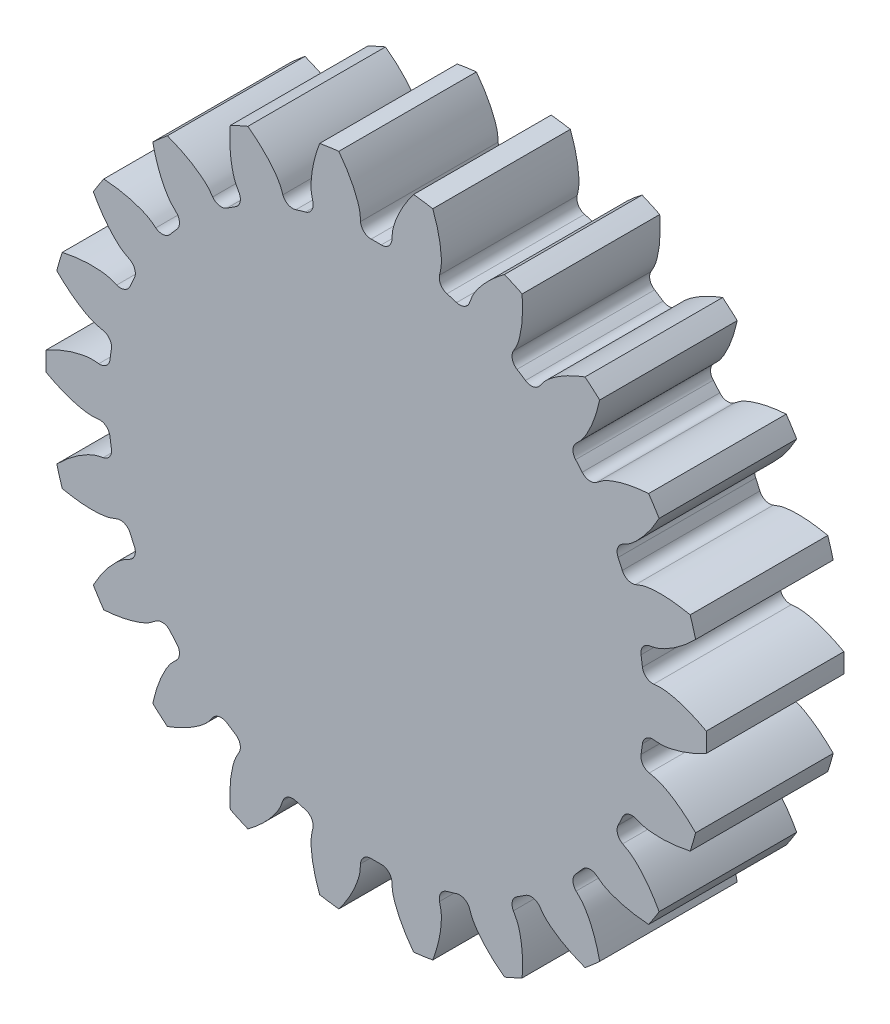
SolidWorks part; units mm, degrees
ref_plane "前视基准面" through (0, 0, 0) normal (0, 0, 1) x (1, 0, 0)
ref_plane "上视基准面" through (0, 0, 0) normal (0, 1, 0) x (1, 0, 0)
ref_plane "右视基准面" through (0, 0, 0) normal (1, 0, 0) x (0, 0, -1)
ref_axis "Axis1" through (0, 0, -88.99) along (0, 0, 1)
sketch "草图1" plane through (0, 0, 0) normal (0, 0, 1) x (1, 0, 0)
  circle A0 centre (0, 0) radius 12
extrude "LaShenA" add sketch "草图1" along normal blind 5
sketch "SketchA" plane through (0, 0, 5) normal (0, 0, 1) x (1, 0, 0)
  line L0 (0, 0) -> (0, 12) construction
  arc A0 (0.1829, 9.7483) -> (-0.1829, 9.7483) centre (0, 0) ccw
  arc A1 (1.7922, 12.4394) -> (-1.7922, 12.4394) centre (0, 0) ccw
  arc A2 (-0.1829, 9.7483) -> (-0.5693, 10.1058) centre (-0.19, 10.1282) cw
  arc A3 (0.5693, 10.1058) -> (0.1829, 9.7483) centre (0.19, 10.1282) cw
  circle A4 centre (0, 0) radius 10.3366 construction
  circle A5 centre (0, 0) radius 12 construction
  circle A6 centre (0, 0) radius 9.75 construction
  circle A7 centre (0, 0) radius 11 construction
  spline S0 degree 3 poles (0.5693, 10.1058) (0.5736, 10.1777) (0.5776, 10.2793) (0.5937, 10.3939) (0.606, 10.4523) (0.6168, 10.4986) (0.6308, 10.5517) (0.6482, 10.6114) (0.6693, 10.6775) (0.6947, 10.75) (0.7246, 10.8287) (0.7593, 10.9132) (0.7992, 11.0036) (0.8447, 11.0994) (0.8959, 11.2005) (0.9533, 11.3067) (1.0172, 11.4176) (1.0878, 11.533) (1.1655, 11.6527) (1.2504, 11.7762) (1.3429, 11.9034) (1.4432, 12.0339) (1.5907, 12.2156) (1.7093, 12.3501) (1.7922, 12.4394) knots 0.122554 0.122554 0.122554 0.122554 0.192705 0.222547 0.235684 0.251209 0.269123 0.289425 0.312116 0.337195 0.364662 0.394518 0.426763 0.461396 0.498418 0.537828 0.579626 0.623813 0.670389 0.719353 0.770705 0.824446 0.880576 1 1 1 1
  spline S1 degree 3 poles (-0.5693, 10.1058) (-0.5736, 10.1777) (-0.5776, 10.2793) (-0.5937, 10.3939) (-0.606, 10.4523) (-0.6168, 10.4986) (-0.6308, 10.5517) (-0.6482, 10.6114) (-0.6693, 10.6775) (-0.6947, 10.75) (-0.7246, 10.8287) (-0.7593, 10.9132) (-0.7992, 11.0036) (-0.8447, 11.0994) (-0.8959, 11.2005) (-0.9533, 11.3067) (-1.0172, 11.4176) (-1.0878, 11.533) (-1.1655, 11.6527) (-1.2504, 11.7762) (-1.3429, 11.9034) (-1.4432, 12.0339) (-1.5907, 12.2156) (-1.7093, 12.3501) (-1.7922, 12.4394) knots 0.122554 0.122554 0.122554 0.122554 0.192705 0.222547 0.235684 0.251209 0.269123 0.289425 0.312116 0.337195 0.364662 0.394518 0.426763 0.461396 0.498418 0.537828 0.579626 0.623813 0.670389 0.719353 0.770705 0.824446 0.880576 1 1 1 1
  dimension "D1" = 0.38
  dimension "Db" = 20.6732
  dimension "Da" = 24
  dimension "Df" = 19.5
  dimension "Dn" = 22
extrude "Cut-ExtrudeA" cut sketch "SketchA" against normal blind 10
pattern_circular "www.KYTool.cn" count 22 over 360 about axis through (0, 0, -88.99) along (0, 0, 1) of "Cut-ExtrudeA"
